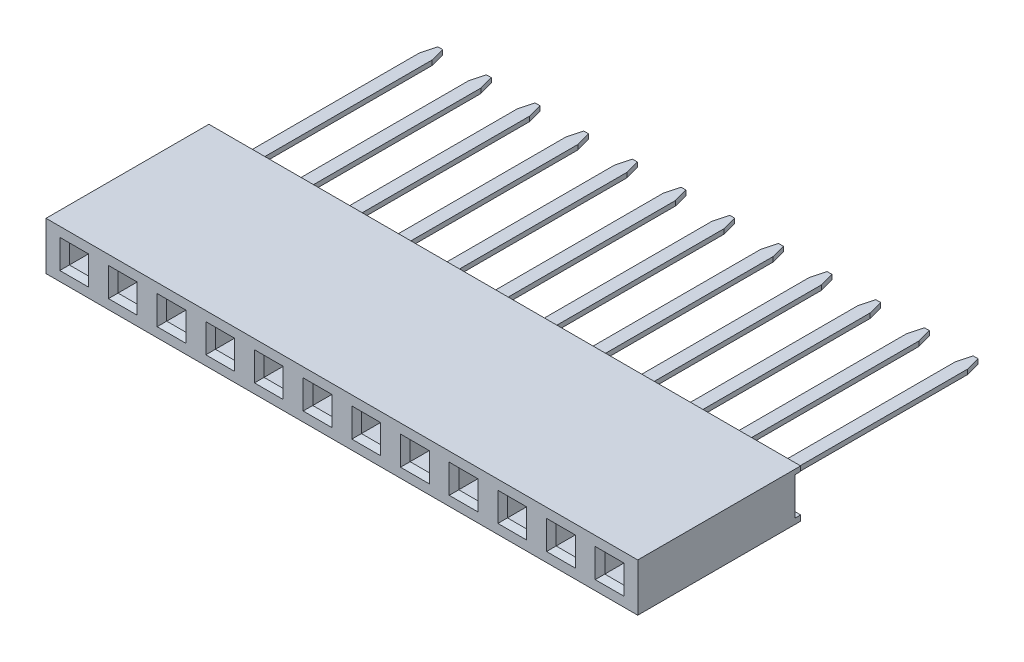
SolidWorks part; units mm, degrees
ref_plane "Front Plane" through (0, 0, 0) normal (0, 0, 1) x (1, 0, 0)
ref_plane "Top Plane" through (0, 0, 0) normal (0, 1, 0) x (1, 0, 0)
ref_plane "Right Plane" through (0, 0, 0) normal (1, 0, 0) x (0, 0, -1)
sketch "Sketch1" plane through (0, 0, 0) normal (0, 0, 1) x (1, 0, 0)
  line L1 (0, 0) -> (30.88, 0)
  line L2 (0, 0) -> (0, 2.5)
  line L3 (0, 2.5) -> (30.88, 2.5)
  line L4 (30.88, 0) -> (30.88, 2.5)
  dimension "width" = 2.5
  dimension "length" = 30.88
extrude "Boss-Extrude1" add sketch "Sketch1" along normal blind 8.5
sketch "Sketch2" plane through (0, 0, 8.5) normal (0, 0, 1) x (1, 0, 0)
  line L0 (0, 1.25) -> (30.88, 1.25) construction
  line L1 (0, 2.5) -> (0, 0) construction
  line L2 (30.88, 0) -> (30.88, 2.5) construction
  line L3 (0, 0) -> (30.88, 0) construction
  line L5 (30.88, 2.5) -> (0, 2.5) construction
  line L6 (1.47, 2.5) -> (1.47, 0) construction
  line L7 (0.97, 1.75) -> (1.97, 1.75)
  line L8 (0.97, 1.75) -> (0.97, 0.75)
  line L9 (0.97, 0.75) -> (1.97, 0.75)
  line L10 (1.97, 1.75) -> (1.97, 0.75)
  point P16 (1.47, 1.75)
  point P17 (1.97, 1.25)
  dimension "D1" = 1.25
  dimension "D2" = 1.47
  dimension "D3" = 1
  dimension "D4" = 1
extrude "Cut-Extrude1" cut sketch "Sketch2" against normal blind 2.25
chamfer "Chamfer1" distance 0.25 angle 45 4 edges at (0.97, 1.25, 8.5) (1.47, 0.75, 8.5) (1.97, 1.25, 8.5) (1.47, 1.75, 8.5)
sketch "Sketch3" plane through (0, 0, 0) normal (-1, 0, 0) x (0, 0, 1)
  line L0 (0, 2.5) -> (0, 0) construction
  line L1 (0, 2.25) -> (0.3, 2.25)
  line L2 (0, 2.25) -> (0, 0.2861)
  line L3 (0, 0.2861) -> (0.3, 0.2861)
  line L4 (0.3, 2.25) -> (0.3, 0.2861)
  line L5 (8.5, 1.25) -> (0, 1.2681) construction
  line L6 (8.5, 2.5) -> (0, 2.5) construction
  line L7 (8.5, 2.5) -> (8.5, 0) construction
  dimension "D1" = 0.25
  dimension "D2" = 0.3
extrude "Cut-Extrude2" cut sketch "Sketch3" against normal through all
ref_plane "Plane1" through (0, 1.25, 0) normal (0, -1, 0) x (-1, 0, 0)
sketch "Sketch4" plane through (0, 1.25, 0) normal (0, -1, 0) x (-1, 0, 0)
  line L0 (-1.47, -8.25) -> (-1.47, -0.3) construction
  line L1 (-0.97, -8.25) -> (-1.97, -8.25) construction
  line L2 (-30.88, -0.3) -> (0, -0.3) construction
  line L3 (0, 0) -> (-30.88, 0) construction
  line L4 (-1.795, -0.3) -> (-1.145, -0.3)
  line L5 (-1.795, -0.3) -> (-1.795, 10.6)
  line L6 (-1.795, 10.6) -> (-1.145, 10.6)
  line L7 (-1.145, -0.3) -> (-1.145, 10.6)
  point P10 (-1.47, -0.3)
  dimension "D1" = 0.65
  dimension "D2" = 10.6
extrude "Boss-Extrude2" add sketch "Sketch4" along normal mid plane 0.25 separate body
chamfer "Chamfer2" distance 0.2 angle 75 2 edges at (1.145, 1.25, -10.6) (1.795, 1.25, -10.6)
pattern_linear "LPattern4" count 12 spacing 2.54 along (1, 0, 0) of bodies 104
pattern_linear "LPattern5" count 12 spacing 2.54 along (1, 0, 0) of "Cut-Extrude1", "Chamfer1"
equation "\"pins\"= 12"
equation "\"rows\"= 1"
equation "\"length\"= 2.54 * \"pins\" + .4"
equation "\"width\"= 2.5 * \"rows\""
equation "\"width@Sketch1\"= 2.5 * \"rows\""
equation "\"length@Sketch1\"= 2.54 * \"pins\" + .4"
equation "\"D2@LPattern5\"= \"rows\""
equation "\"D2@LPattern4\"= \"rows\""
equation "\"D1@LPattern4\"= \"pins\""
equation "\"D1@LPattern5\"= \"pins\""
